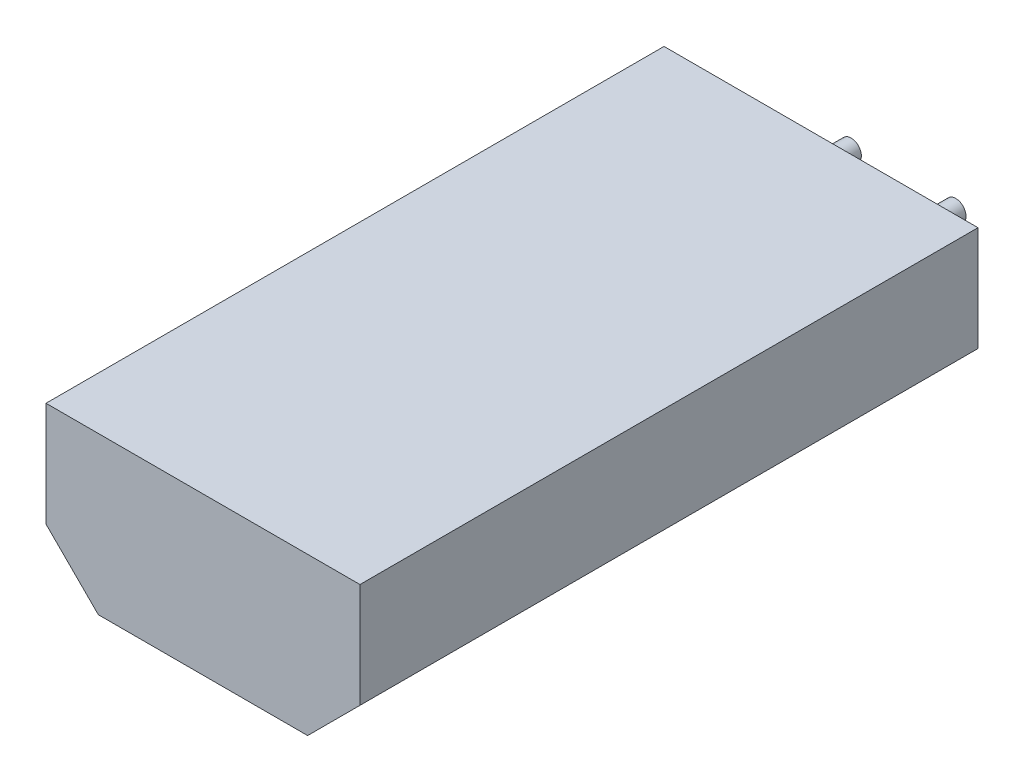
SolidWorks part; units mm, degrees
ref_plane "Front Plane" through (0, 0, 0) normal (0, 0, 1) x (1, 0, 0)
ref_plane "Top Plane" through (0, 0, 0) normal (0, 1, 0) x (1, 0, 0)
ref_plane "Right Plane" through (0, 0, 0) normal (1, 0, 0) x (0, 0, -1)
sketch "Sketch1" plane through (0, 0, 0) normal (0, 0, 1) x (1, 0, 0)
  line L0 (-2.54, 1.905) -> (-2.54, -0.635)
  line L1 (-2.54, -0.635) -> (-1.27, -1.905)
  line L2 (-1.27, -1.905) -> (3.81, -1.905)
  line L3 (3.81, -1.905) -> (5.08, -0.635)
  line L4 (5.08, -0.635) -> (5.08, 1.905)
  line L5 (5.08, 1.905) -> (-2.54, 1.905)
extrude "Component_Outline" add sketch "Sketch1" along normal blind 15 separate body
sketch "Sketch2" plane through (0, 0, 0) normal (0, 0, 1) x (1, 0, 0)
  circle A0 centre (0, 0) radius 0.25
extrude "1" add sketch "Sketch2" against normal blind 2 separate body
sketch "Sketch3" plane through (0, 0, 0) normal (0, 0, 1) x (1, 0, 0)
  circle A0 centre (2.54, 0) radius 0.25
extrude "2" add sketch "Sketch3" against normal blind 2 separate body
sketch3d "3DSketch1"
  line L0 (0, 0, 0) -> (1, 0, 0)
  line L1 (0, 0, 0) -> (0, 1, 0)
  line L2 (0, 0, 0) -> (0, 0, 1)
  point P0 (0, 0, 0)
